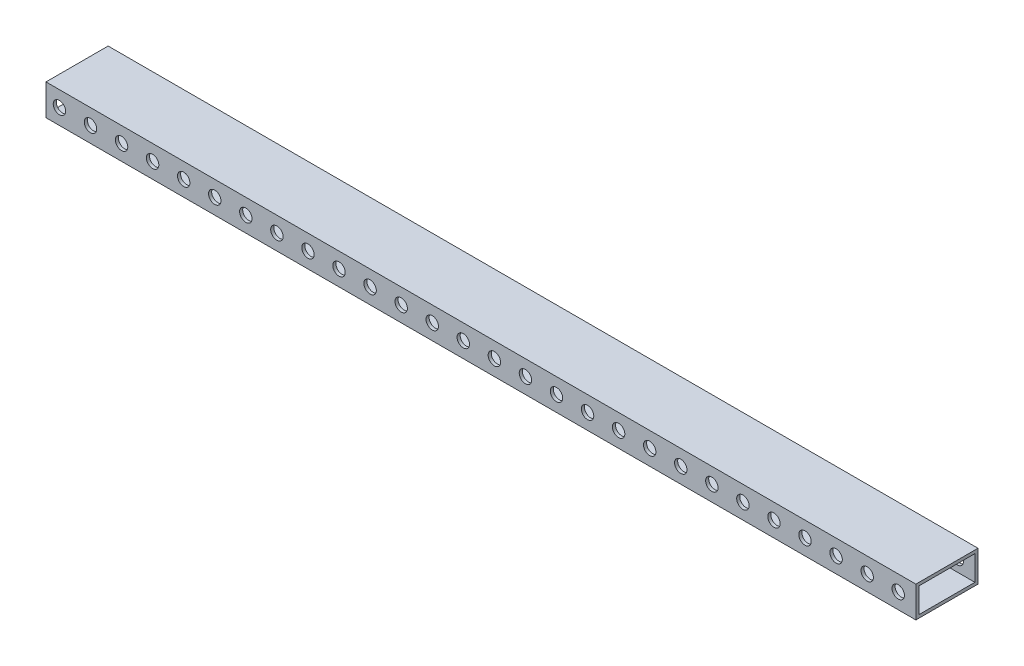
SolidWorks part; units mm, degrees
ref_plane "Front Plane" through (0, 0, 0) normal (0, 0, 1) x (1, 0, 0)
ref_plane "Top Plane" through (0, 0, 0) normal (0, 1, 0) x (1, 0, 0)
ref_plane "Right Plane" through (0, 0, 0) normal (1, 0, 0) x (0, 0, -1)
sketch "Sketch3" plane through (0, 0, 0) normal (1, 0, 0) x (0, 0, -1)
  line L0 (-17.5388, 8.1604) -> (28.1812, 8.1604)
  line L1 (-20.0788, 10.7004) -> (30.7212, 10.7004)
  line L2 (-20.0788, 10.7004) -> (-20.0788, -14.6996)
  line L3 (-20.0788, -14.6996) -> (30.7212, -14.6996)
  line L4 (30.7212, 10.7004) -> (30.7212, -14.6996)
  line L5 (28.1812, 8.1604) -> (28.1812, -12.1596)
  line L6 (-17.5388, -12.1596) -> (28.1812, -12.1596)
  line L7 (-17.5388, 8.1604) -> (-17.5388, -12.1596)
  dimension "D1" = 50.8
  dimension "D3" = 25.4
  dimension "D2" = 2.54
extrude "Boss-Extrude1" add sketch "Sketch3" along normal blind 711.2 contours L2 L1 L4 L3 | L0 L5 L6 L7
sketch "Sketch5" plane through (0, 0, 20.0788) normal (0, 0, 1) x (1, 0, 0)
  line L0 (711.2, 10.7004) -> (0, 10.7004) construction
  circle A0 centre (10.9788, -1.9996) radius 5.08
  circle A1 centre (36.3788, -1.9996) radius 5.08
  circle A2 centre (61.7788, -1.9996) radius 5.08
  circle A3 centre (87.1788, -1.9996) radius 5.08
  circle A4 centre (112.5788, -1.9996) radius 5.08
  circle A5 centre (137.9788, -1.9996) radius 5.08
  circle A6 centre (163.3788, -1.9996) radius 5.08
  circle A7 centre (188.7788, -1.9996) radius 5.08
  circle A8 centre (214.1788, -1.9996) radius 5.08
  circle A9 centre (239.5788, -1.9996) radius 5.08
  circle A10 centre (264.9788, -1.9996) radius 5.08
  circle A11 centre (290.3788, -1.9996) radius 5.08
  circle A12 centre (315.7788, -1.9996) radius 5.08
  circle A13 centre (341.1788, -1.9996) radius 5.08
  circle A14 centre (366.5788, -1.9996) radius 5.08
  circle A15 centre (391.9788, -1.9996) radius 5.08
  circle A16 centre (417.3788, -1.9996) radius 5.08
  circle A17 centre (442.7788, -1.9996) radius 5.08
  circle A18 centre (468.1788, -1.9996) radius 5.08
  circle A19 centre (493.5788, -1.9996) radius 5.08
  circle A20 centre (518.9788, -1.9996) radius 5.08
  circle A21 centre (544.3788, -1.9996) radius 5.08
  circle A22 centre (569.7788, -1.9996) radius 5.08
  circle A23 centre (595.1788, -1.9996) radius 5.08
  circle A24 centre (620.5788, -1.9996) radius 5.08
  circle A25 centre (645.9788, -1.9996) radius 5.08
  circle A26 centre (671.3788, -1.9996) radius 5.08
  circle A27 centre (696.7788, -1.9996) radius 5.08
  dimension "D1" = 12.7
  dimension "D2" = 28
extrude "Cut-Extrude2" cut sketch "Sketch5" against normal blind 127 contours A0 | A1 | A3 | A2 | A4 | A6 | A5 | A7 | A8 | A9 | A10 | A11 | A12 | A13 | A14 | A15 | A16 | A17 | A19 | A20 | A18 | A21 | A22 | A23 | A24 | A26 | A27 | A25
